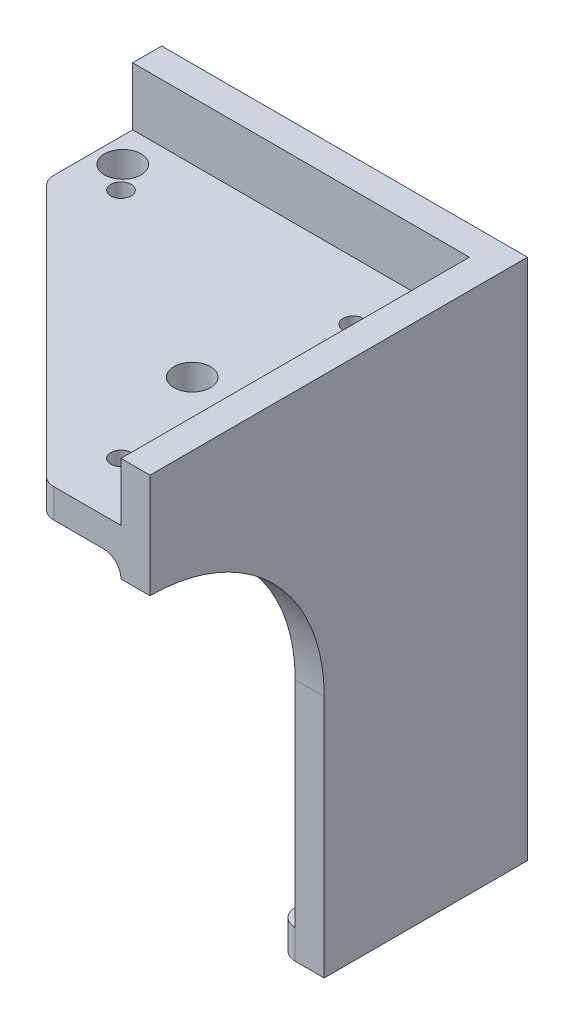
SolidWorks part; units mm, degrees
ref_plane "Alzado" through (0, 0, 0) normal (0, 0, 1) x (1, 0, 0)
ref_plane "Planta" through (0, 0, 0) normal (0, 1, 0) x (1, 0, 0)
ref_plane "Vista lateral" through (0, 0, 0) normal (1, 0, 0) x (0, 0, -1)
sketch "Croquis1" plane through (0, 0, 0) normal (0, 0, 1) x (1, 0, 0)
  line L0 (-63, 0) -> (0, 0)
  line L1 (0, 0) -> (0, -90)
  line L2 (0, -90) -> (-33, -90)
  line L3 (-33, -90) -> (-33, -48)
  line L6 (-63, -18) -> (-63, 0)
  arc A0 (-33, -48) -> (-63, -18) centre (-63, -48) ccw
  dimension "D1" = 60
  dimension "D2" = 33
  dimension "D3" = 90
  dimension "D4" = 63
  dimension "D5" = 42
extrude "Saliente-Extruir1" add sketch "Croquis1" along normal blind 5 separate body
sketch "Croquis2" plane through (0, 0, 5) normal (0, 0, 1) x (1, 0, 0)
  line L1 (0, 0) -> (-5, 0)
  line L2 (0, 0) -> (0, -90)
  line L3 (0, -90) -> (-5, -90)
  line L4 (-5, 0) -> (-5, -90)
  line L5 (0, -90) -> (0, 0) construction
  line L6 (0, 0) -> (-63, 0) construction
  line L7 (-33, -90) -> (0, -90) construction
  dimension "D1" = 5
extrude "Saliente-Extruir2" add sketch "Croquis2" along normal blind 60
sketch "Croquis3" plane through (0, 0, 0) normal (1, 0, 0) x (0, 0, -1)
  line L0 (-65, -90) -> (-35, -90)
  line L1 (-35, -90) -> (-35, -48)
  line L2 (-65, -90) -> (-65, -18)
  line L3 (-65, -90) -> (-65, 0) construction
  line L4 (-65, -90) -> (0, -90) construction
  arc A0 (-35, -48) -> (-65, -18) centre (-65, -48) ccw
  dimension "D3" = 60
  dimension "D1" = 30
  dimension "D2" = 72
extrude "Cortar-Extruir1" cut sketch "Croquis3" against normal up to surface (5 mm away) up to face at (-5, -33.75, 50)
sketch "Croquis4" plane through (0, -90, 0) normal (0, -1, 0) x (1, 0, 0)
  line L0 (-33, 8) -> (-8, 8)
  line L1 (-33, 5) -> (-5, 5)
  line L2 (-33, 5) -> (-33, 8)
  line L3 (-8, 35) -> (-5, 35)
  line L4 (-5, 5) -> (-5, 35)
  line L5 (-8, 8) -> (-8, 35)
  line L6 (-33, 5) -> (-5, 5) construction
  line L7 (-5, 35) -> (-5, 5) construction
  line L8 (-5, 35) -> (0, 35) construction
  line L9 (-33, 5) -> (-33, 0) construction
  dimension "D1" = 3
extrude "Saliente-Extruir3" add sketch "Croquis4" against normal blind 5
fillet "Redondeo1" radius 3 2 edges at (-33, -87.5, 8) (-8, -87.5, 35)
sketch "Croquis5" plane through (0, 0, 5) normal (0, 0, 1) x (1, 0, 0)
  line L0 (-5, 0) -> (-63, 0) construction
  line L1 (-5, -10) -> (-63, -10)
  line L2 (-5, -10) -> (-5, -15)
  line L3 (-5, -15) -> (-63, -15)
  line L4 (-63, -10) -> (-63, -15)
  line L6 (-63, 0) -> (-63, -18) construction
  line L7 (-5, 0) -> (-5, -85) construction
  dimension "D1" = 10
  dimension "D2" = 5
extrude "Saliente-Extruir4" add sketch "Croquis5" along normal up to surface (60 mm away) up to face at (-2.5, -9, 65)
sketch "Croquis6" plane through (0, -10, 0) normal (0, 1, 0) x (1, 0, 0)
  line L0 (-63, -19.8176) -> (-17.8176, -65)
  line L1 (-63, -65) -> (-63, -5) construction
  line L2 (-63, -65) -> (-5, -65) construction
  line L3 (-17.8176, -65) -> (-63, -65)
  line L4 (-63, -65) -> (-63, -19.8176)
  line L5 (-5, -5) -> (-63, -5) construction
  line L6 (-5, -65) -> (-5, -5) construction
  circle A0 centre (-60, -18.575) radius 3 construction
  dimension "D1" = 6
  dimension "D2" = 45
  dimension "D3" = 13.575
extrude "Cortar-Extruir2" cut sketch "Croquis6" against normal up to surface (5 mm away) up to face at (-34, -15, 35)
fillet "Redondeo2" radius 3 2 edges at (-17.8176, -12.5, 65) (-63, -12.5, 19.8176)
fillet "Redondeo3" radius 3 3 edges at (-34, -15, 5) (-5, -15, 35)
sketch "Croquis7" plane through (0, -10, 0) normal (0, 1, 0) x (1, 0, 0)
  line L0 (-5, -5) -> (-63, -5) construction
  line L1 (-5, -65) -> (-5, -5) construction
  line L2 (-63, -18.575) -> (-63, -5) construction
  circle A0 centre (-15, -55) radius 1.75
  circle A1 centre (-15, -15) radius 1.75
  circle A2 centre (-55, -15) radius 1.75
  circle A3 centre (-58.7, -11) radius 3.15
  circle A4 centre (-20.975, -36.7557) radius 3.15
  dimension "D1" = 3.5
  dimension "D2" = 40
  dimension "D3" = 40
  dimension "D4" = 10
  dimension "D5" = 10
  dimension "D6" = 6.3
  dimension "D7" = 6.3
  dimension "D8" = 6
  dimension "D9" = 4.3
  dimension "D10" = 31.7557
  dimension "D11" = 15.975
extrude "Cortar-Extruir3" cut sketch "Croquis7" against normal up to surface (5 mm away) up to face at (-34.2416, -15, 35.6701)
